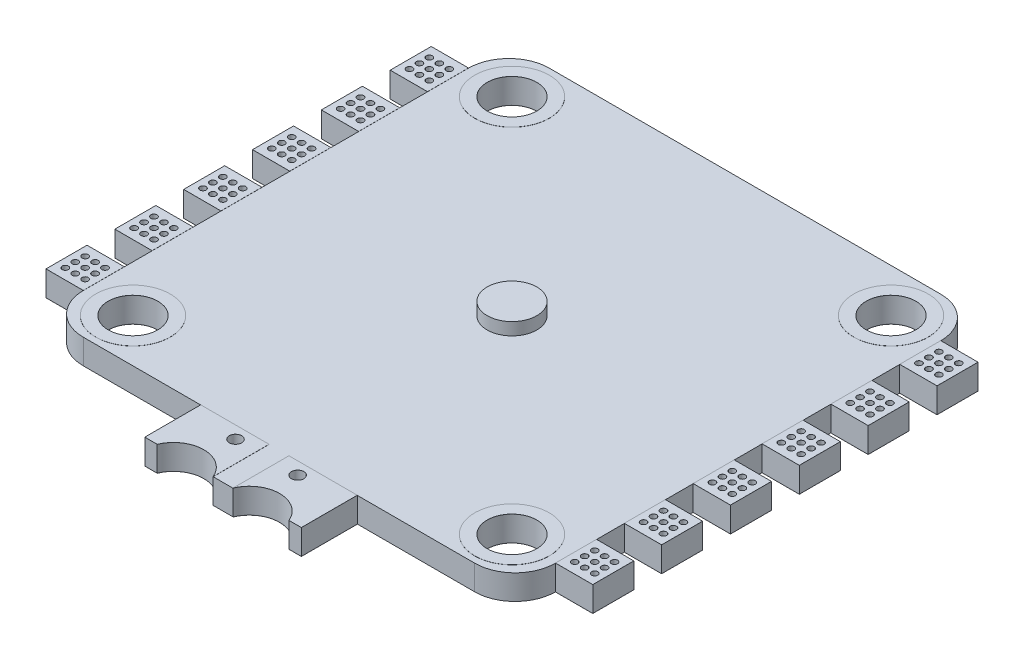
SolidWorks part; units mm, degrees
ref_plane "Front" through (0, 0, 0) normal (0, 0, 1) x (1, 0, 0)
ref_plane "Top" through (0, 0, 0) normal (0, 1, 0) x (1, 0, 0)
ref_plane "Right" through (0, 0, 0) normal (1, 0, 0) x (0, 0, -1)
sketch "Sketch1" plane through (0, 0, 0) normal (0, 1, 0) x (1, 0, 0)
  line L1 (19, -18.75) -> (-19, -18.75)
  line L2 (19, -18.75) -> (19, 18.75)
  line L3 (19, 18.75) -> (-19, 18.75)
  line L4 (-19, -18.75) -> (-19, 18.75)
  line L5 (19, -18.75) -> (-19, 18.75) construction
  line L6 (19, 18.75) -> (-19, -18.75) construction
  circle A0 centre (-15.25, 15.25) radius 2
  circle A1 centre (15.25, 15.25) radius 2
  circle A2 centre (15.25, -15.25) radius 2
  circle A3 centre (-15.25, -15.25) radius 2
  point P0 (0, 0)
  point P14 (15.25, -10.8624)
  dimension "D3" = 4
  dimension "D1" = 38
  dimension "D2" = 37.5
  dimension "D4" = 30.5
  dimension "D5" = 30.5
  dimension "D6" = 15.25
  dimension "D7" = 15.25
extrude "Boss-Extrude1" add sketch "Sketch1" along normal mid plane 2
fillet "Fillet1" radius 3.25 4 edges at (-19, 0, -18.75) (19, 0, -18.75) (-19, 0, 18.75) (19, 0, 18.75)
sketch "Sketch2" plane through (0, 1, 0) normal (0, 1, 0) x (1, 0, 0)
  line L0 (-19, 6.66) -> (-22, 6.66)
  line L1 (-19, 15.5) -> (-22, 15.5)
  line L2 (-19, 15.5) -> (-19, 12.2)
  line L3 (-19, 12.2) -> (-22, 12.2)
  line L4 (-22, 15.5) -> (-22, 12.2)
  line L5 (-19, 9.96) -> (-19, 6.66)
  line L6 (-22, 9.96) -> (-22, 6.66)
  line L7 (-19, 9.96) -> (-22, 9.96)
  line L8 (-19, 1.12) -> (-22, 1.12)
  line L9 (-19, 4.42) -> (-19, 1.12)
  line L10 (-22, 4.42) -> (-22, 1.12)
  line L11 (-19, 4.42) -> (-22, 4.42)
  line L12 (-19, -4.42) -> (-22, -4.42)
  line L13 (-19, -1.12) -> (-19, -4.42)
  line L14 (-22, -1.12) -> (-22, -4.42)
  line L15 (-19, -1.12) -> (-22, -1.12)
  line L16 (-19, -9.96) -> (-22, -9.96)
  line L17 (-19, -6.66) -> (-19, -9.96)
  line L18 (-22, -6.66) -> (-22, -9.96)
  line L19 (-19, -6.66) -> (-22, -6.66)
  line L20 (-19, -15.5) -> (-22, -15.5)
  line L21 (-19, -12.2) -> (-19, -15.5)
  line L22 (-22, -12.2) -> (-22, -15.5)
  line L23 (-19, -12.2) -> (-22, -12.2)
  dimension "D1" = 3.3
  dimension "D2" = 22
  dimension "D4" = 2.24
  dimension "D3" = 6
extrude "Boss-Extrude2" add sketch "Sketch2" against normal up to surface (2 mm away) up to face at (0, -1, 0)
mirror "Mirror1" about plane through (0, 0, 0) normal (1, 0, 0) of "Boss-Extrude2"
sketch "Sketch3" plane through (0, 1, 0) normal (0, 1, 0) x (1, 0, 0)
  line L0 (-15.75, -18.75) -> (15.75, -18.75) construction
  line L1 (-6.3, -18.75) -> (6.3, -18.75)
  line L2 (-6.3, -18.75) -> (-6.3, -23.25)
  line L3 (-6.3, -23.25) -> (-5.3, -23.25)
  line L4 (6.3, -18.75) -> (6.3, -23.25)
  line L5 (15.75, 18.75) -> (-15.75, 18.75) construction
  line L6 (-3.05, -21.75) -> (3.05, -21.75) construction
  line L7 (-0.8, -23.25) -> (0.8, -23.25)
  line L8 (-5.3, -23.25) -> (-0.8, -23.25) construction
  line L9 (5.3, -23.25) -> (6.3, -23.25)
  line L10 (0.8, -23.25) -> (5.3, -23.25) construction
  line L11 (-3.05, -24.1875) -> (3.05, -24.1875) construction
  arc A0 (-0.8, -23.25) -> (-5.3, -23.25) centre (-3.05, -24.1875) ccw
  arc A1 (5.3, -23.25) -> (0.8, -23.25) centre (3.05, -24.1875) ccw
  arc A2 (-5.3, -23.25) -> (-0.8, -23.25) centre (-3.05, -24.1875) ccw construction
  arc A3 (0.8, -23.25) -> (5.3, -23.25) centre (3.05, -24.1875) ccw construction
  point P6 (0, -24.1875)
  point P16 (-0.8, -23.25)
  point P17 (-5.3, -23.25)
  dimension "D4" = 4.5
  dimension "D1" = 12.6
  dimension "D2" = 42
  dimension "D3" = 1.5
  dimension "D5" = 1
extrude "Boss-Extrude3" add sketch "Sketch3" against normal up to surface (2 mm away) up to face at (0, -1, 0)
sketch "Sketch4" plane through (0, 1, 0) normal (0, 1, 0) x (1, 0, 0)
  circle A0 centre (-15.25, -15.25) radius 2 construction
  circle A1 centre (15.25, -15.25) radius 2 construction
  circle A2 centre (15.25, 15.25) radius 2 construction
  circle A3 centre (-15.25, 15.25) radius 2 construction
  circle A4 centre (-15.25, -15.25) radius 2
  circle A5 centre (15.25, -15.25) radius 2
  circle A6 centre (15.25, 15.25) radius 2
  circle A7 centre (-15.25, 15.25) radius 2
  circle A8 centre (-15.25, 15.25) radius 3
  circle A9 centre (15.25, 15.25) radius 3
  circle A10 centre (15.25, -15.25) radius 3
  circle A11 centre (-15.25, -15.25) radius 3
  dimension "D1" = 1
extrude "Boss-Extrude4" add sketch "Sketch4" along normal blind 0.01 separate body
mirror "Mirror2" about plane through (0, 0, 0) normal (0, 1, 0) of bodies 105 108 107 106
sketch "Sketch5" plane through (0, 1, 0) normal (0, 1, 0) x (1, 0, 0)
  line L0 (-19, -12.2) -> (-22, -12.2) construction
  line L1 (-22, -12.2) -> (-22, -15.5) construction
  circle A0 centre (-20.5, -13.85) radius 0.25 construction
  circle A1 centre (-21.3, -14.65) radius 0.25
  circle A2 centre (-20.5, -14.65) radius 0.25
  circle A3 centre (-19.7, -14.65) radius 0.25
  circle A4 centre (-20.5, -13.85) radius 0.25
  circle A5 centre (-19.7, -13.85) radius 0.25
  circle A6 centre (-20.5, -13.05) radius 0.25
  circle A7 centre (-19.7, -13.05) radius 0.25
  circle A8 centre (-21.3, -13.85) radius 0.25
  circle A9 centre (-21.3, -13.05) radius 0.25
  point P5 (-20.5, -12.2)
  point P9 (-22, -13.85)
  dimension "D1" = 0.5
  dimension "D2" = 0.8
  dimension "D3" = 0.8
  dimension "D6" = 0.8
  dimension "D7" = 0.8
  dimension "D4" = 3
  dimension "D5" = 3
extrude "Cut-Extrude1" cut sketch "Sketch5" against normal through all both and the other way through all
sketch "Sketch6" plane through (0, 1, 0) normal (0, 1, 0) x (1, 0, 0)
  line L0 (-22, -12.2) -> (-22, -15.5) construction
  line L1 (-22, -15.5) -> (-19, -15.5) construction
  line L2 (-19, -12.2) -> (-22, -12.2) construction
  line L3 (-22, -12.2) -> (-22, -15.5)
  line L4 (-22, -15.5) -> (-19, -15.5)
  line L5 (-19, -12.2) -> (-22, -12.2)
  line L6 (-19, -15.5) -> (-19, -12.2)
  circle A0 centre (-19.7, -13.05) radius 0.25 construction
  circle A1 centre (-20.5, -13.05) radius 0.25 construction
  circle A2 centre (-20.5, -13.85) radius 0.25 construction
  circle A3 centre (-19.7, -13.85) radius 0.25 construction
  circle A4 centre (-19.7, -14.65) radius 0.25 construction
  circle A5 centre (-20.5, -14.65) radius 0.25 construction
  circle A6 centre (-21.3, -14.65) radius 0.25 construction
  circle A7 centre (-21.3, -13.85) radius 0.25 construction
  circle A8 centre (-21.3, -13.05) radius 0.25 construction
  circle A9 centre (-19.7, -13.05) radius 0.25
  circle A10 centre (-20.5, -13.05) radius 0.25
  circle A11 centre (-20.5, -13.85) radius 0.25
  circle A12 centre (-19.7, -13.85) radius 0.25
  circle A13 centre (-19.7, -14.65) radius 0.25
  circle A14 centre (-20.5, -14.65) radius 0.25
  circle A15 centre (-21.3, -14.65) radius 0.25
  circle A16 centre (-21.3, -13.85) radius 0.25
  circle A17 centre (-21.3, -13.05) radius 0.25
extrude "Boss-Extrude5" add sketch "Sketch6" along normal blind 0.01 separate body
pattern_linear "LPattern10" count 6 spacing 5.54 along (0, 0, -1) of "Cut-Extrude1"
mirror "Mirror3" about plane through (0, 0, 0) normal (1, 0, 0) of "Cut-Extrude1", "LPattern10"
pattern_linear "LPattern11" count 6 spacing 5.54 along (0, 0, -1) of bodies 116
mirror "Mirror4" about plane through (0, 0, 0) normal (1, 0, 0) of bodies 116 121 120 119 118 117 115
delete or keep bodies "Body-Delete/Keep 1" type delete bodies bodies 128
mirror "Mirror5" about plane through (0, 0, 0) normal (0, 1, 0) of bodies 117 127 126 125 124 123 122 121 120 119 118 116
sketch "Sketch7" plane through (0, 1, 0) normal (0, 1, 0) x (1, 0, 0)
  line L0 (-0.8, -23.25) -> (0.8, -23.25) construction
  circle A0 centre (-2.5, -19.75) radius 0.5
  circle A1 centre (2.5, -19.75) radius 0.5
  dimension "D1" = 1
  dimension "D2" = 5
  dimension "D3" = 2.5
  dimension "D4" = 3.5
extrude "Cut-Extrude2" cut sketch "Sketch7" against normal through all both and the other way through all
sketch "Sketch8" plane through (0, 1, 0) normal (0, 1, 0) x (1, 0, 0)
  line L0 (5.3, -23.25) -> (6.3, -23.25) construction
  line L1 (6.3, -23.25) -> (6.3, -18.75) construction
  line L2 (-6.3, -23.25) -> (-5.3, -23.25) construction
  line L3 (-0.8, -23.25) -> (0.8, -23.25) construction
  line L4 (-6.3, -18.75) -> (-6.3, -23.25) construction
  line L5 (5.3, -23.25) -> (6.3, -23.25)
  line L6 (6.3, -23.25) -> (6.3, -18.75)
  line L7 (-6.3, -23.25) -> (-5.3, -23.25)
  line L8 (-0.8, -23.25) -> (0.8, -23.25) construction
  line L9 (-6.3, -18.75) -> (-6.3, -23.25)
  line L10 (-6.3, -18.75) -> (-0.8, -18.75)
  line L11 (-0.8, -23.25) -> (-0.8, -18.75)
  line L12 (0.8, -23.25) -> (0.8, -18.75)
  line L13 (0.8, -18.75) -> (6.3, -18.75)
  line L14 (-0.8, -18.75) -> (0.8, -18.75) construction
  arc A0 (5.3, -23.25) -> (0.8, -23.25) centre (3.05, -24.1875) ccw construction
  arc A1 (-0.8, -23.25) -> (-5.3, -23.25) centre (-3.05, -24.1875) ccw construction
  arc A2 (5.3, -23.25) -> (0.8, -23.25) centre (3.05, -24.1875) ccw
  arc A3 (-0.8, -23.25) -> (-5.3, -23.25) centre (-3.05, -24.1875) ccw
  circle A4 centre (2.5, -19.75) radius 0.5 construction
  circle A5 centre (-2.5, -19.75) radius 0.5 construction
  circle A6 centre (2.5, -19.75) radius 0.5
  circle A7 centre (-2.5, -19.75) radius 0.5
extrude "Boss-Extrude6" add sketch "Sketch8" along normal blind 0.01 separate body
mirror "Mirror6" about plane through (0, 0, 0) normal (0, 1, 0) of bodies 142 143
sketch "Sketch9" plane through (0, 1, 0) normal (0, 1, 0) x (1, 0, 0)
  circle A0 centre (0, 0) radius 2
  dimension "D1" = 4
extrude "Boss-Extrude7" add sketch "Sketch9" along normal blind 1 separate body
